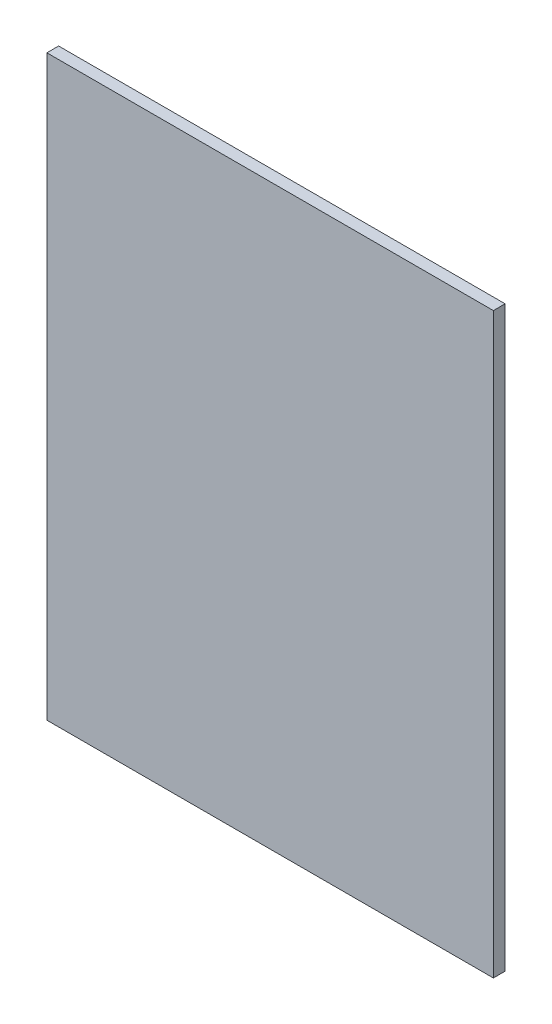
SolidWorks part; units mm, degrees
ref_plane "Front Plane" through (0, 0, 0) normal (0, 0, 1) x (1, 0, 0)
ref_plane "Top Plane" through (0, 0, 0) normal (0, 1, 0) x (1, 0, 0)
ref_plane "Right Plane" through (0, 0, 0) normal (1, 0, 0) x (0, 0, -1)
sketch "Sketch1" plane through (0, 0, 0) normal (0, 0, 1) x (1, 0, 0)
  line L1 (31.2345, 47.2529) -> (-65.2855, 47.2529)
  line L3 (-65.2855, 47.2529) -> (-65.2855, -77.6926)
  line L4 (-65.2855, -77.6926) -> (31.2345, -77.6926)
  line L5 (31.2345, -77.6926) -> (31.2345, 47.2529)
  point P1 (-63.5389, 48.8397)
  point P6 (33.0766, 47.2529)
  point P7 (29.7445, 47.2529)
extrude "Boss-Extrude1" add sketch "Sketch1" along normal blind 2.54
